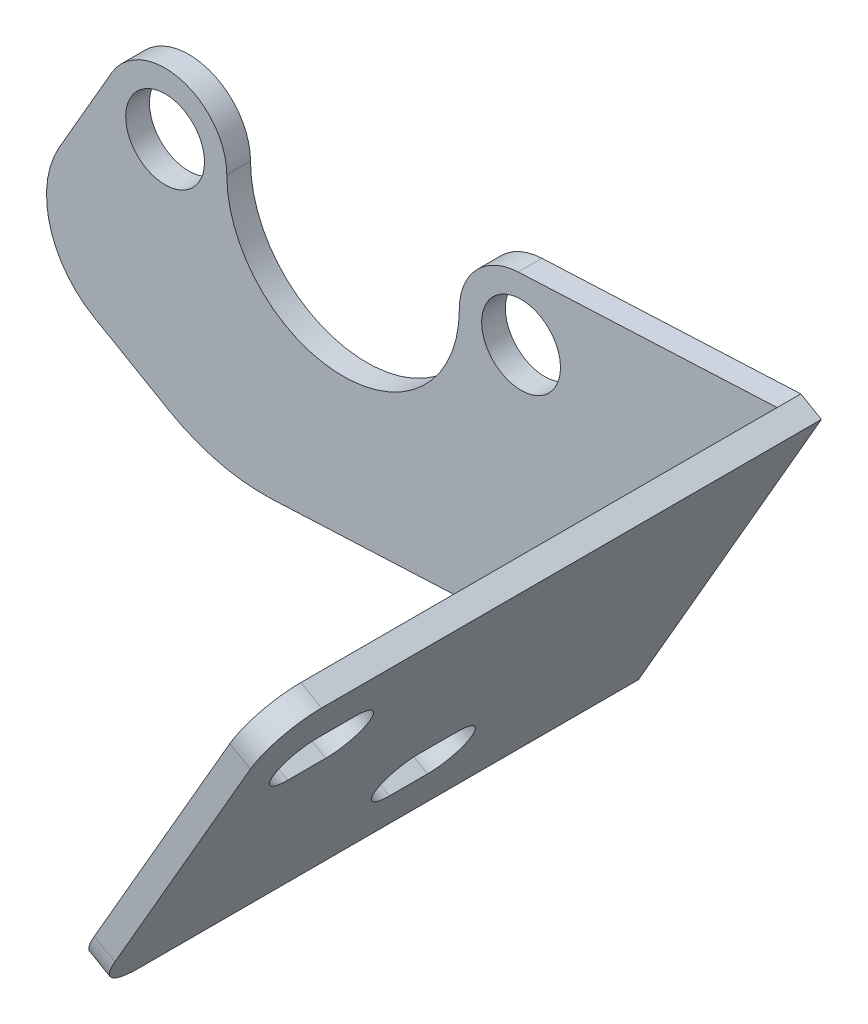
SolidWorks part; units mm, degrees
material "1023 Carbon Steel Sheet (SS)"
ref_plane "Front Plane" through (0, 0, 0) normal (0, 0, 1) x (1, 0, 0)
ref_plane "Top Plane" through (0, 0, 0) normal (0, 1, 0) x (1, 0, 0)
ref_plane "Right Plane" through (0, 0, 0) normal (1, 0, 0) x (0, 0, -1)
sketch "Sketch3" plane through (0, 0, 0) normal (0, 0, 1) x (1, 0, 0)
  line L0 (-30.949, 3.7275) -> (-44.3098, -19.4139)
  line L1 (179.172, 111.2384) -> (135.178, 136.6384) construction
  line L2 (58.0837, 9.4573) -> (23.4415, 7.8461)
  line L3 (146.2905, 155.8858) -> (16.1155, -69.5839) construction
  line L4 (-44.3098, -19.4139) -> (-16.8134, -35.2889)
  line L6 (80.347, -59.9315) -> (36.353, -34.5315) construction
  line L7 (60.8334, 7.8698) -> (36.353, -34.5315)
  line L8 (60.8334, 7.8698) -> (-13.6708, 50.8848) construction
  line L9 (60.8334, 7.8698) -> (58.0837, 9.4573)
  line L10 (36.353, -34.5315) -> (33.6033, -32.944)
  line L11 (33.6033, -32.944) -> (-16.8134, -35.2889)
  circle A0 centre (23.825, -0.4) radius 5.2705 construction
  circle A1 centre (-23.8, -0.4) radius 5.2705 construction
  circle A2 centre (23.825, -0.4) radius 5.2705
  circle A3 centre (-23.8, -0.4) radius 5.2705
  arc A4 (-14.275, -0.4) -> (-23.8, 9.125) centre (-23.8, -0.4) ccw construction
  arc A5 (23.825, 9.125) -> (14.3, -0.4) centre (23.825, -0.4) ccw construction
  arc A6 (-14.275, -0.4) -> (14.3, -0.4) centre (0.0125, -0.4) ccw construction
  arc A7 (-14.275, -0.4) -> (-23.8, 9.125) centre (-23.8, -0.4) ccw construction
  arc A8 (23.825, 9.125) -> (14.3, -0.4) centre (23.825, -0.4) ccw construction
  arc A9 (-14.275, -0.4) -> (14.3, -0.4) centre (0.0125, -0.4) ccw construction
  circle A10 centre (23.825, -0.4) radius 8.255
  arc A11 (-15.545, -0.4) -> (15.57, -0.4) centre (0.0125, -0.4) ccw
  circle A12 centre (-23.8, -0.4) radius 8.255
  arc A13 (23.825, 7.855) -> (15.57, -0.4) centre (23.825, -0.4) ccw construction
  arc A14 (-15.545, -0.4) -> (-23.8, 7.855) centre (-23.8, -0.4) ccw construction
  dimension "D2" = 90
  dimension "D3" = 31.75
  dimension "D4" = 76.2
  dimension "D5" = 3.175
  dimension "D6" = 3.175
  dimension "D1" = 1.27
extrude "Boss-Extrude1" add sketch "Sketch3" along normal up to surface (3.175 mm away)
sketch "Sketch4" plane through (0, 0, 3.175) normal (0, 0, 1) x (1, 0, 0)
  line L0 (60.8334, 7.8698) -> (36.353, -34.5315)
  line L1 (60.8334, 7.8698) -> (58.0837, 9.4573)
  line L2 (36.353, -34.5315) -> (33.6033, -32.944)
  line L3 (58.0837, 9.4573) -> (33.6033, -32.944)
  line L4 (146.2905, 155.8858) -> (16.1155, -69.5839) construction
  line L6 (58.0837, 9.4573) -> (60.8334, 7.8698) construction
  dimension "D1" = 3.175
extrude "Boss-Extrude2" add sketch "Sketch4" along normal up to surface (70.05 mm away)
fillet "Fillet1" radius 12.7 1 edges at (-44.3098, -19.4139, 1.5875)
fillet "Fillet3" radius 25.4 1 edges at (-16.8134, -35.2889, 1.5875)
sketch "Sketch5" plane through (39.4677, -22.7867, 0) normal (-0.866, 0.5, 0) x (0, 0, 1)
  line L0 (73.225, -11.7287) -> (73.225, 37.2322) construction
  line L1 (73.225, 37.2322) -> (3.175, 37.2322) construction
  line L2 (35.125, 0.9713) -> (37.665, 0.9713) construction
  line L3 (22.425, 208.1463) -> (22.425, -52.2037) construction
  line L4 (73.225, -11.7287) -> (3.175, -11.7287) construction
  line L5 (35.125, 0.9713) -> (32.585, 0.9713) construction
  line L6 (32.585, 4.9401) -> (37.665, 4.9401)
  line L7 (32.585, -2.9974) -> (37.665, -2.9974)
  line L8 (60.525, 24.5322) -> (57.985, 24.5322) construction
  line L9 (60.525, 24.5322) -> (63.065, 24.5322) construction
  line L10 (57.985, 28.5009) -> (63.065, 28.5009)
  line L11 (57.985, 20.5634) -> (63.065, 20.5634)
  circle A0 centre (60.525, 24.5322) radius 3.9687 construction
  circle A1 centre (35.125, 0.9713) radius 3.9687 construction
  circle A2 centre (32.585, 0.9713) radius 3.9687
  circle A3 centre (37.665, 0.9713) radius 3.9687
  circle A4 centre (57.985, 24.5322) radius 3.9687
  circle A5 centre (63.065, 24.5322) radius 3.9687
  dimension "D1" = 7.9375
  dimension "D2" = 12.7
  dimension "D3" = 12.7
  dimension "D4" = 12.7
  dimension "D5" = 12.7
  dimension "D6" = 2.54
  dimension "D7" = 2.54
  dimension "D8" = 2.54
  dimension "D9" = 2.54
extrude "Cut-Extrude1" cut sketch "Sketch5" against normal blind 6.35 contours A5 A4 | A5 A4 | A5 A4 L11 | A4 A5 | A5 L10 A4 | A3 A2 | A2 A3 | A3 A2 | A3 L6 A2 | A3 A2 L7
fillet "Fillet4" radius 6.35 2 edges at (59.4586, 8.6636, 73.225) (34.9781, -33.7377, 73.225)
ref_plane "Plane1" through (0, 0, 98.625) normal (0, 0, 1) x (1, 0, 0)
